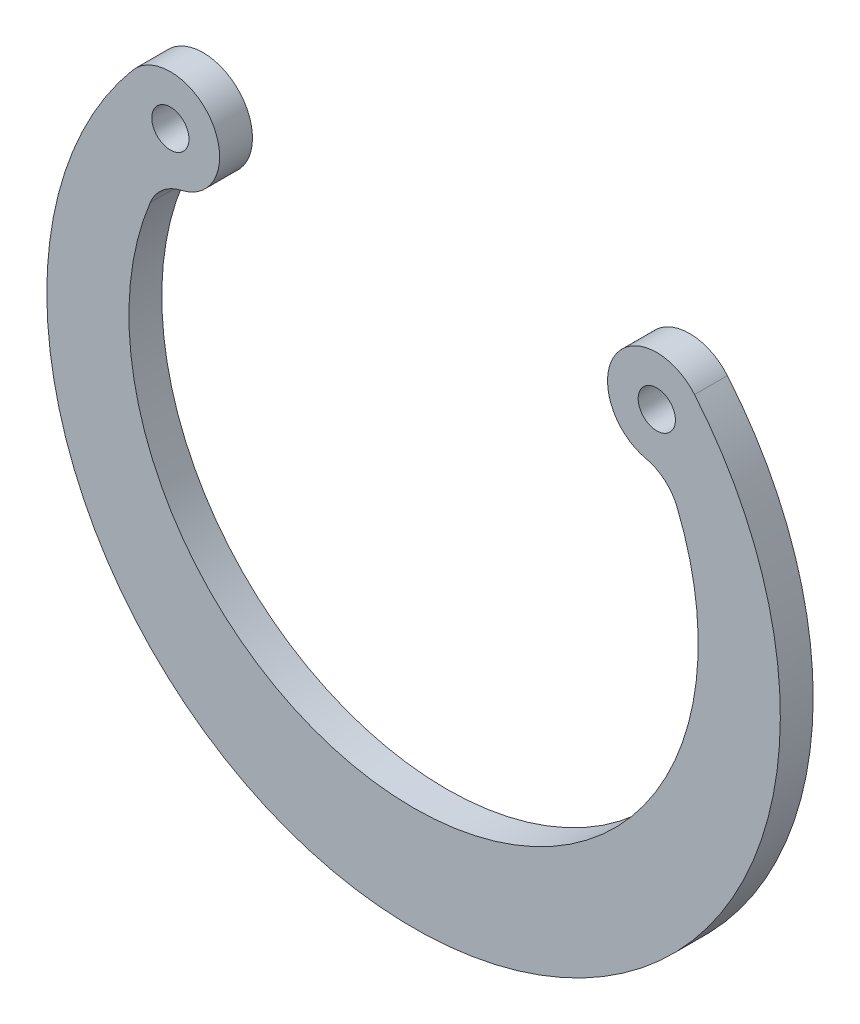
SolidWorks part; units mm, degrees
ref_plane "Спереди" through (0, 0, 0) normal (0, 0, 1) x (1, 0, 0)
ref_plane "Сверху" through (0, 0, 0) normal (0, 1, 0) x (1, 0, 0)
ref_plane "Справа" through (0, 0, 0) normal (1, 0, 0) x (0, 0, -1)
sketch "Эскиз1" plane through (0, 0, 0) normal (0, 0, 1) x (1, 0, 0)
  line L0 (0, 1) -> (0, 0)
  line L1 (-11.1076, 9.3204) -> (0, 0) construction
  line L2 (0, 0) -> (11.1076, 9.3204) construction
  line L3 (-11.1076, 9.3204) -> (11.1076, 9.3204) construction
  arc A0 (-12.8312, 10.7667) -> (12.8312, 10.7667) centre (0, 0) ccw
  arc A1 (12.8312, 10.7667) -> (10.6152, 7.125) centre (11.1076, 9.3204) ccw
  arc A2 (10.6152, 7.125) -> (12.028, 5.9323) centre (10.1775, 5.1734) cw
  arc A3 (12.028, 5.9323) -> (-12.028, 5.9323) centre (0, 1) cw
  arc A4 (-12.028, 5.9323) -> (-10.6152, 7.125) centre (-10.1775, 5.1734) cw
  arc A5 (-10.6152, 7.125) -> (-12.8312, 10.7667) centre (-11.1076, 9.3204) ccw
  circle A6 centre (-11.1076, 9.3204) radius 0.85
  circle A7 centre (11.1076, 9.3204) radius 0.85
  circle A8 centre (0, 0) radius 16.75 construction
  dimension "D1" = 33.5
  dimension "D3" = 1.7
  dimension "D4" = 1.7
  dimension "D5" = 2.25
  dimension "D6" = 2.25
  dimension "D8" = 13
  dimension "D9" = 2
  dimension "D10" = 2
  dimension "D2" = 1
  dimension "D7" = 100
extrude "Бобышка-Вытянуть1" add sketch "Эскиз1" against normal blind 1.5 contours A4 A5 A0 A1 A2 A3 A6 A7
